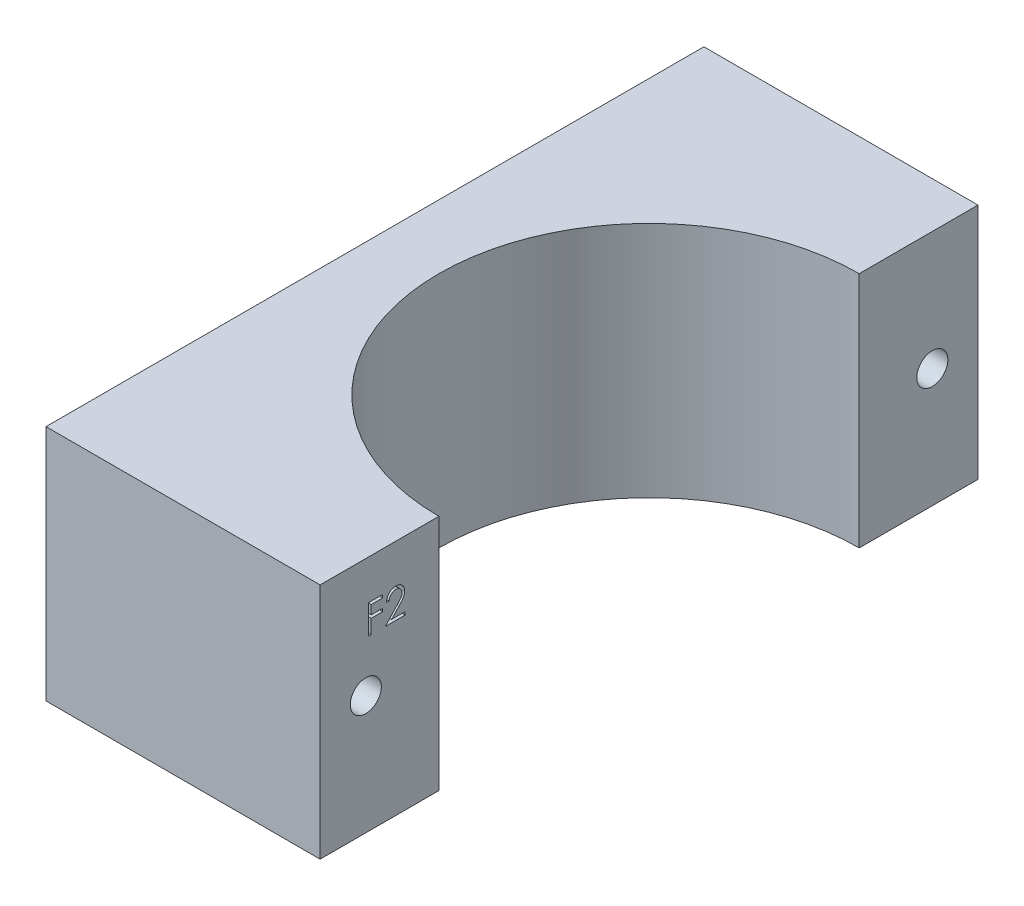
SolidWorks part; units mm, degrees
ref_plane "Front Plane" through (0, 0, 0) normal (0, 0, 1) x (1, 0, 0)
ref_plane "Top Plane" through (0, 0, 0) normal (0, 1, 0) x (1, 0, 0)
ref_plane "Right Plane" through (0, 0, 0) normal (1, 0, 0) x (0, 0, -1)
sketch "Sketch1" plane through (0, 0, 0) normal (0, 1, 0) x (1, 0, 0)
  line L0 (-46.9983, 32.5286) -> (-46.9983, -39.4714)
  line L1 (-46.9983, -39.4714) -> (-16.9983, -39.4714)
  line L2 (-16.9983, -39.4714) -> (-16.9983, -26.4714)
  line L3 (-46.9983, 32.5286) -> (-16.9983, 32.5286)
  line L4 (-16.9983, 32.5286) -> (-16.9983, 19.5286)
  arc A0 (-16.9983, 19.5286) -> (-16.9983, -26.4714) centre (-16.9983, -3.4714) ccw
  dimension "D1" = 72
  dimension "D2" = 30
  dimension "D3" = 30
  dimension "D4" = 13
  dimension "D5" = 13
extrude "Boss-Extrude1" add sketch "Sketch1" along normal blind 26
sketch "Sketch2" plane through (-16.9983, 0, 0) normal (1, 0, 0) x (0, 0, -1)
  line L0 (-34.4714, 26) -> (-34.4714, 0) construction
  line L1 (-39.4714, 26) -> (-26.4714, 26) construction
  line L2 (-39.4714, 0) -> (-26.4714, 0) construction
  line L3 (27.5286, 26) -> (27.5286, 0) construction
  line L4 (19.5286, 26) -> (32.5286, 26) construction
  line L5 (19.5286, 0) -> (32.5286, 0) construction
  line L6 (-39.4714, 26) -> (-39.4714, 0) construction
  line L7 (32.5286, 26) -> (32.5286, 0) construction
  circle A0 centre (-34.4714, 13) radius 1.7
  circle A1 centre (27.5286, 13) radius 1.7
  dimension "D1" = 5
  dimension "D2" = 5
extrude "Cut-Extrude1" cut sketch "Sketch2" against normal through all
sketch "Sketch3" plane through (-16.9983, 0, 0) normal (1, 0, 0) x (0, 0, -1)
  text T0 "F2"
extrude "Cut-Extrude2" cut sketch "Sketch3" against normal blind 1
